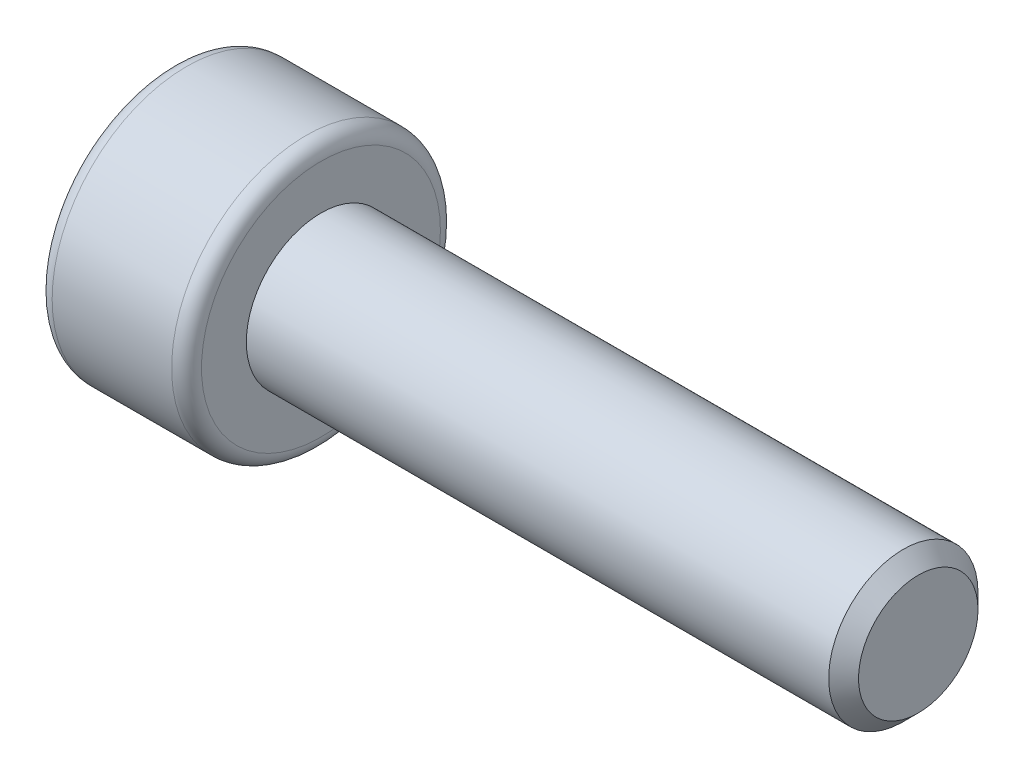
SolidWorks part; units mm, degrees
ref_plane "前视基准面" through (0, 0, 0) normal (0, 0, 1) x (1, 0, 0)
ref_plane "上视基准面" through (0, 0, 0) normal (0, 1, 0) x (1, 0, 0)
ref_plane "右视基准面" through (0, 0, 0) normal (1, 0, 0) x (0, 0, -1)
sketch "草图1" plane through (0, 0, 0) normal (0, 0, 1) x (1, 0, 0)
  line L0 (-5, 0) -> (-5, 1.8)
  line L1 (-5, 1.8) -> (-3, 1.8)
  line L2 (-3, 1.8) -> (-3, 1)
  line L3 (-3, 1) -> (5, 1)
  line L4 (5, 1) -> (5, 0)
  line L5 (5, 0) -> (-5, 0) construction
  line L6 (-5, 0) -> (5, 0)
  dimension "D1" = 3.6
  dimension "D2" = 2
  dimension "D3" = 2
  dimension "D4" = 8
revolve "旋转1" add sketch "草图1" angle 360 about L5
sketch "草图2" plane through (-5, 0, 0) normal (-1, 0, 0) x (0, 0, 1)
  line L1 (0.866, 0) -> (0.433, 0.75)
  line L2 (0.433, 0.75) -> (-0.433, 0.75)
  line L3 (-0.433, 0.75) -> (-0.866, 0)
  line L4 (-0.866, 0) -> (-0.433, -0.75)
  line L5 (-0.433, -0.75) -> (0.433, -0.75)
  line L6 (0.433, -0.75) -> (0.866, 0)
  circle A0 centre (0, 0) radius 0.75 construction
  dimension "D1" = 1.5
extrude "切除-拉伸1" cut sketch "草图2" against normal blind 1.5
fillet "圆角1" radius 0.2 2 edges at (-3, 0, -1.8) (-5, 0, -1.8)
chamfer "倒角1" distance 0.2 angle 45 1 edges at (5, 0, -1)
